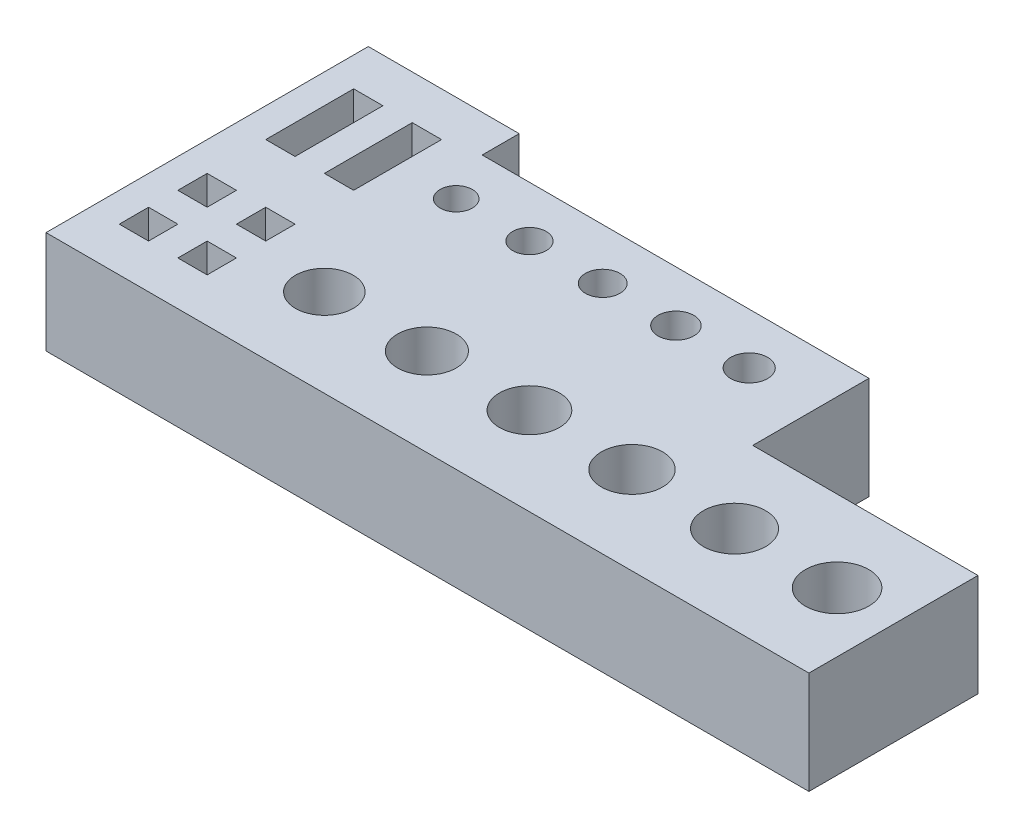
SolidWorks part; units mm, degrees
ref_plane "Front Plane" through (0, 0, 0) normal (0, 0, 1) x (1, 0, 0)
ref_plane "Top Plane" through (0, 0, 0) normal (0, 1, 0) x (1, 0, 0)
ref_plane "Right Plane" through (0, 0, 0) normal (1, 0, 0) x (0, 0, -1)
sketch "Sketch1" plane through (0, 0, 0) normal (0, 1, 0) x (1, 0, 0)
  line L0 (0, 0) -> (66.137, 0)
  line L1 (0, 0) -> (0, 27.94)
  line L2 (66.137, 0) -> (66.137, 27.94)
  line L3 (0, 27.94) -> (66.137, 27.94)
  line L4 (0, 20.32) -> (66.137, 20.32) construction
  line L5 (0, 7.62) -> (66.137, 7.62) construction
  line L6 (5.08, 8.89) -> (7.62, 6.35) construction
  line L7 (2.54, 24.13) -> (5.08, 24.13)
  line L8 (2.54, 24.13) -> (2.54, 16.51)
  line L9 (2.54, 16.51) -> (5.08, 16.51)
  line L10 (5.08, 24.13) -> (5.08, 16.51)
  line L11 (7.62, 24.13) -> (10.16, 24.13)
  line L12 (7.62, 24.13) -> (7.62, 16.51)
  line L13 (7.62, 16.51) -> (10.16, 16.51)
  line L14 (10.16, 24.13) -> (10.16, 16.51)
  line L15 (2.54, 11.43) -> (5.08, 11.43)
  line L16 (2.54, 11.43) -> (2.54, 8.89)
  line L17 (2.54, 8.89) -> (5.08, 8.89)
  line L18 (5.08, 11.43) -> (5.08, 8.89)
  line L19 (7.62, 11.43) -> (10.16, 11.43)
  line L20 (7.62, 11.43) -> (7.62, 8.89)
  line L21 (7.62, 8.89) -> (10.16, 8.89)
  line L22 (10.16, 11.43) -> (10.16, 8.89)
  line L23 (2.54, 6.35) -> (5.08, 6.35)
  line L24 (2.54, 6.35) -> (2.54, 3.81)
  line L25 (2.54, 3.81) -> (5.08, 3.81)
  line L26 (5.08, 6.35) -> (5.08, 3.81)
  line L27 (7.62, 6.35) -> (10.16, 6.35)
  line L28 (7.62, 6.35) -> (7.62, 3.81)
  line L29 (7.62, 3.81) -> (10.16, 3.81)
  line L30 (10.16, 6.35) -> (10.16, 3.81)
  line L31 (5.08, 24.13) -> (7.62, 16.51) construction
  line L32 (6.35, 20.32) -> (6.35, 7.62) construction
  circle A0 centre (15.24, 20.32) radius 1.4
  circle A1 centre (21.59, 20.32) radius 1.45
  circle A2 centre (27.94, 20.32) radius 1.5
  circle A3 centre (34.29, 20.32) radius 1.55
  circle A4 centre (40.64, 20.32) radius 1.6
  circle A5 centre (16.51, 7.62) radius 2.5
  circle A6 centre (25.4, 7.62) radius 2.55
  circle A7 centre (34.29, 7.62) radius 2.6
  circle A8 centre (43.18, 7.62) radius 2.65
  circle A9 centre (52.07, 7.62) radius 2.7
  circle A10 centre (60.96, 7.62) radius 2.75
  point P33 (6.35, 7.62)
  point P34 (6.35, 20.32)
  point P59 (53.6834, 7.62)
  point P60 (6.35, 7.62)
  dimension "D22" = 2.8
  dimension "D23" = 2.9
  dimension "D24" = 3
  dimension "D25" = 3.1
  dimension "D26" = 3.2
  dimension "D32" = 5
  dimension "D33" = 5.1
  dimension "D34" = 5.2
  dimension "D35" = 5.3
  dimension "D36" = 5.4
  dimension "D37" = 5.5
  dimension "D1" = 2.54
  dimension "D2" = 2.54
  dimension "D3" = 2.54
  dimension "D4" = 2.54
  dimension "D5" = 2.54
  dimension "D6" = 2.54
  dimension "D7" = 2.54
  dimension "D8" = 2.54
  dimension "D9" = 2.54
  dimension "D10" = 2.54
  dimension "D11" = 2.54
  dimension "D12" = 2.54
  dimension "D13" = 7.62
  dimension "D14" = 7.62
  dimension "D15" = 2.54
  dimension "D16" = 2.54
  dimension "D17" = 2.54
  dimension "D18" = 7.62
  dimension "D19" = 7.62
  dimension "D20" = 12.7
  dimension "D21" = 6.35
  dimension "D27" = 5.08
  dimension "D28" = 6.35
  dimension "D29" = 6.35
  dimension "D30" = 6.35
  dimension "D31" = 6.35
  dimension "D38" = 8.89
  dimension "D39" = 6.35
  dimension "D40" = 8.89
  dimension "D41" = 8.89
  dimension "D42" = 8.89
  dimension "D43" = 8.89
extrude "Boss-Extrude1" add sketch "Sketch1" along normal blind 8.89
sketch "Sketch2" plane through (0, 8.89, 0) normal (0, 1, 0) x (1, 0, 0)
  line L0 (66.137, 27.94) -> (0, 27.94) construction
  line L1 (46.6106, 27.94) -> (66.137, 27.94)
  line L2 (46.6106, 27.94) -> (46.6106, 14.6588)
  line L3 (46.6106, 14.6588) -> (66.137, 14.6588)
  line L4 (66.137, 27.94) -> (66.137, 14.6588)
  line L5 (13.0804, 27.94) -> (46.6106, 27.94)
  line L6 (13.0804, 27.94) -> (13.0804, 24.7333)
  line L7 (13.0804, 24.7333) -> (46.6106, 24.7333)
  line L8 (46.6106, 27.94) -> (46.6106, 24.7333)
  line M16 (66.137, 0) -> (66.137, 27.94)
  line M17 (66.137, 27.94) -> (0, 27.94)
extrude "Cut-Extrude1" cut sketch "Sketch2" against normal through all contours L6 L7 L2 M17 | L2 L3 M16 M17
